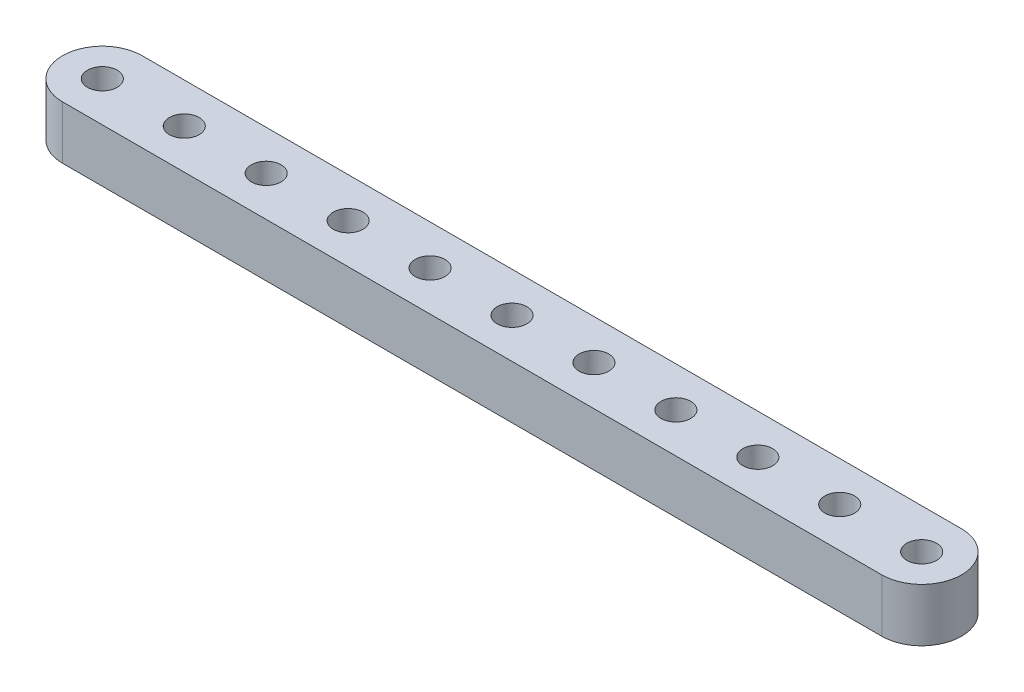
SolidWorks part; units mm, degrees
ref_plane "Front Plane" through (0, 0, 0) normal (0, 0, 1) x (1, 0, 0)
ref_plane "Top Plane" through (0, 0, 0) normal (0, 1, 0) x (1, 0, 0)
ref_plane "Right Plane" through (0, 0, 0) normal (1, 0, 0) x (0, 0, -1)
ref_plane "Plane1" through (0, 0, 0) normal (0, -1, 0) x (1, 0, 0)
sketch "Sketch1" plane through (0, 0, 0) normal (0, -1, 0) x (1, 0, 0)
  line L0 (-48.895, -4.7625) -> (48.895, -4.7625)
  line L1 (48.895, 4.7625) -> (-48.895, 4.7625)
  arc A0 (48.895, -4.7625) -> (48.895, 4.7625) centre (48.895, 0) ccw
  arc A1 (-48.895, 4.7625) -> (-48.895, -4.7625) centre (-48.895, 0) ccw
  circle A2 centre (48.895, 0) radius 1.778
  circle A3 centre (39.116, 0) radius 1.778
  circle A4 centre (29.337, 0) radius 1.778
  circle A5 centre (19.558, 0) radius 1.778
  circle A6 centre (9.779, 0) radius 1.778
  circle A7 centre (0, 0) radius 1.778
  circle A8 centre (-9.779, 0) radius 1.778
  circle A9 centre (-19.558, 0) radius 1.778
  circle A10 centre (-29.337, 0) radius 1.778
  circle A11 centre (-39.116, 0) radius 1.778
  circle A12 centre (-48.895, 0) radius 1.778
extrude "Boss-Extrude1" add sketch "Sketch1" against normal blind 6.35
